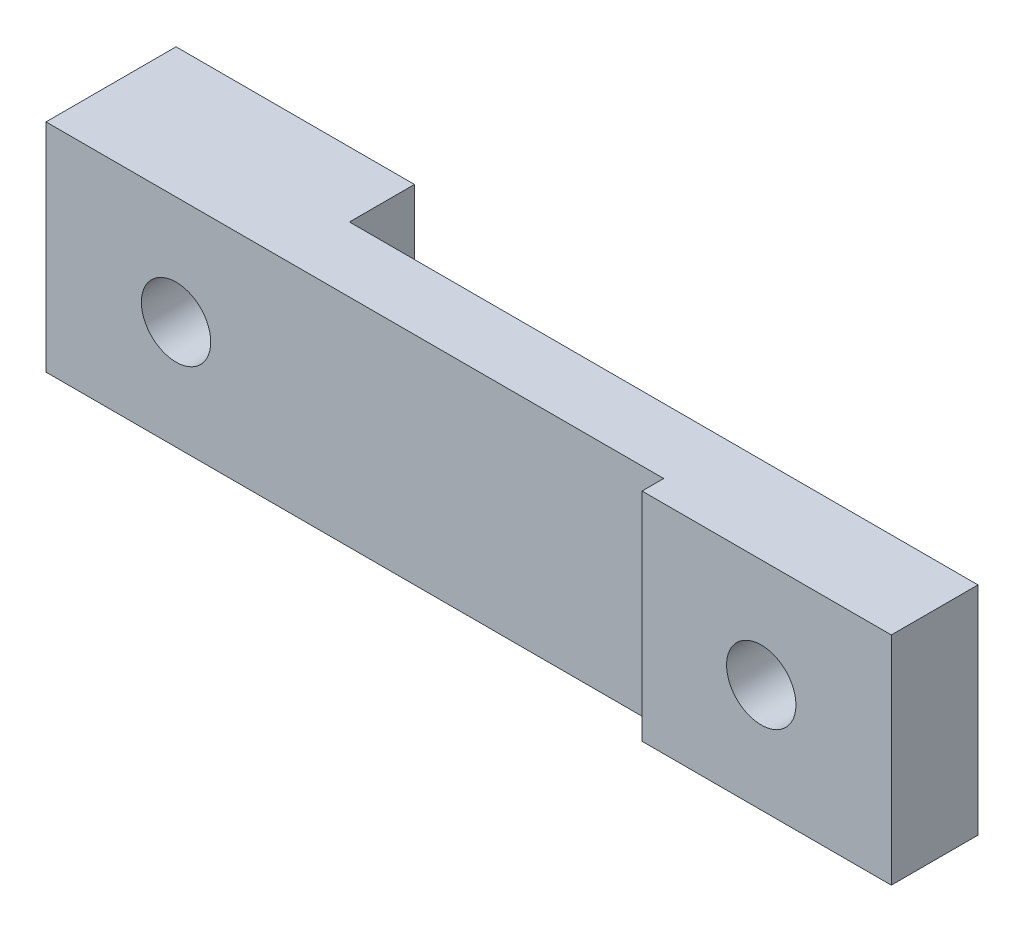
SolidWorks part; units mm, degrees
ref_plane "前基準面" through (0, 0, 0) normal (0, 0, 1) x (1, 0, 0)
ref_plane "上基準面" through (0, 0, 0) normal (0, 1, 0) x (1, 0, 0)
ref_plane "右基準面" through (0, 0, 0) normal (1, 0, 0) x (0, 0, -1)
sketch "草圖1" plane through (0, 0, 0) normal (0, 0, 1) x (1, 0, 0)
  line L1 (-17.5, 5) -> (17.5, 5)
  line L2 (-17.5, 5) -> (-17.5, -5)
  line L3 (-17.5, -5) -> (17.5, -5)
  line L4 (17.5, 5) -> (17.5, -5)
  line L5 (-17.5, 5) -> (17.5, -5) construction
  line L6 (-17.5, -5) -> (17.5, 5) construction
  point P0 (0, 0)
  dimension "D1" = 35
  dimension "D2" = 10
extrude "填料-伸長1" add sketch "草圖1" along normal blind 3
sketch "草圖2" plane through (0, 0, 3) normal (0, 0, 1) x (1, 0, 0)
  line L1 (-18.3462, 0) -> (19.8328, 0) construction
  line L3 (8.5, 5) -> (17.5, 5)
  line L4 (8.5, 5) -> (8.5, -5)
  line L5 (8.5, -5) -> (17.5, -5)
  line L6 (17.5, 5) -> (17.5, -5)
  line L10 (8.5, 5) -> (17.5, -5) construction
  line L11 (8.5, -5) -> (17.5, 5) construction
  point P2 (13, 0)
  dimension "D1" = 9
extrude "填料-伸長2" add sketch "草圖2" along normal blind 1
sketch "草圖3" plane through (0, 0, 4) normal (0, 0, 1) x (1, 0, 0)
  line L0 (-1.3415, 0) -> (19.8328, 0) construction
  line L1 (17.5, -5) -> (17.5, 5) construction
  circle A0 centre (14, 0) radius 1
  dimension "D1" = 2
  dimension "D2" = 3.5
extrude "填料-伸長3" add sketch "草圖3" along normal blind 8
sketch "草圖4" plane through (0, 0, 0) normal (0, 0, -1) x (-1, 0, 0)
  line L0 (-17.8749, 0) -> (21.1381, 0) construction
  line L2 (11.5, 5) -> (17.5, 5)
  line L3 (11.5, 5) -> (11.5, -5)
  line L4 (11.5, -5) -> (17.5, -5)
  line L5 (17.5, 5) -> (17.5, -5)
  line L6 (11.5, 5) -> (17.5, -5) construction
  line L7 (11.5, -5) -> (17.5, 5) construction
  point P3 (14.5, 0)
  dimension "D1" = 6
extrude "填料-伸長4" add sketch "草圖4" along normal blind 3
sketch "草圖5" plane through (0, 0, -3) normal (0, 0, -1) x (-1, 0, 0)
  line L0 (-12.9076, 0) -> (21.2468, 0) construction
  line L1 (17.5, -5) -> (17.5, 5) construction
  circle A0 centre (14, 0) radius 1.5
  dimension "D1" = 3
  dimension "D2" = 3.5
extrude "除料-伸長1" cut sketch "草圖5" against normal blind 6
sketch "草圖6" plane through (-17.5, 0, 0) normal (-1, 0, 0) x (0, 0, 1)
  line L1 (-3, 5) -> (3, 5)
  line L2 (-3, 5) -> (-3, -5)
  line L3 (-3, -5) -> (3, -5)
  line L4 (3, 5) -> (3, -5)
  line L5 (-3, 5) -> (3, -5) construction
  line L6 (-3, -5) -> (3, 5) construction
  point P0 (0, 0)
extrude "填料-伸長5" add sketch "草圖6" along normal blind 5
sketch "草圖7" plane through (0, 0, 4) normal (0, 0, 1) x (1, 0, 0)
  circle A0 centre (14, 0) radius 1.6
  dimension "D1" = 3.2
extrude "除料-伸長2" cut sketch "草圖7" against normal blind 4 and the other way blind 8
sketch "草圖8" plane through (17.5, 0, 0) normal (1, 0, 0) x (0, 0, -1)
  line L1 (-4, 5) -> (0, 5)
  line L2 (-4, 5) -> (-4, -5)
  line L3 (-4, -5) -> (0, -5)
  line L4 (0, 5) -> (0, -5)
  line L5 (-4, 5) -> (0, -5) construction
  line L6 (-4, -5) -> (0, 5) construction
  point P0 (-2, 0)
  dimension "D1" = 4
  dimension "D2" = 10
extrude "填料-伸長6" add sketch "草圖8" along normal blind 2.5
sketch "草圖10" plane through (0, 0, -3) normal (0, 0, -1) x (-1, 0, 0)
  circle A0 centre (14, 0) radius 1.6
  dimension "D1" = 3.2
extrude "除料-伸長3" cut sketch "草圖10" against normal blind 7
sketch "草圖11" plane through (-11.5, 0, 0) normal (1, 0, 0) x (0, 0, -1)
  line L1 (0, 5) -> (3, 5)
  line L2 (0, 5) -> (0, -5)
  line L3 (0, -5) -> (3, -5)
  line L4 (3, 5) -> (3, -5)
extrude "填料-伸長7" add sketch "草圖11" along normal blind 2.5
sketch "草圖12" plane through (-22.5, 0, 0) normal (-1, 0, 0) x (0, 0, 1)
  line L1 (-3, 5) -> (3, 5)
  line L2 (-3, 5) -> (-3, -5)
  line L3 (-3, -5) -> (3, -5)
  line L4 (3, 5) -> (3, -5)
extrude "除料-伸長4" cut sketch "草圖12" against normal blind 2.5
